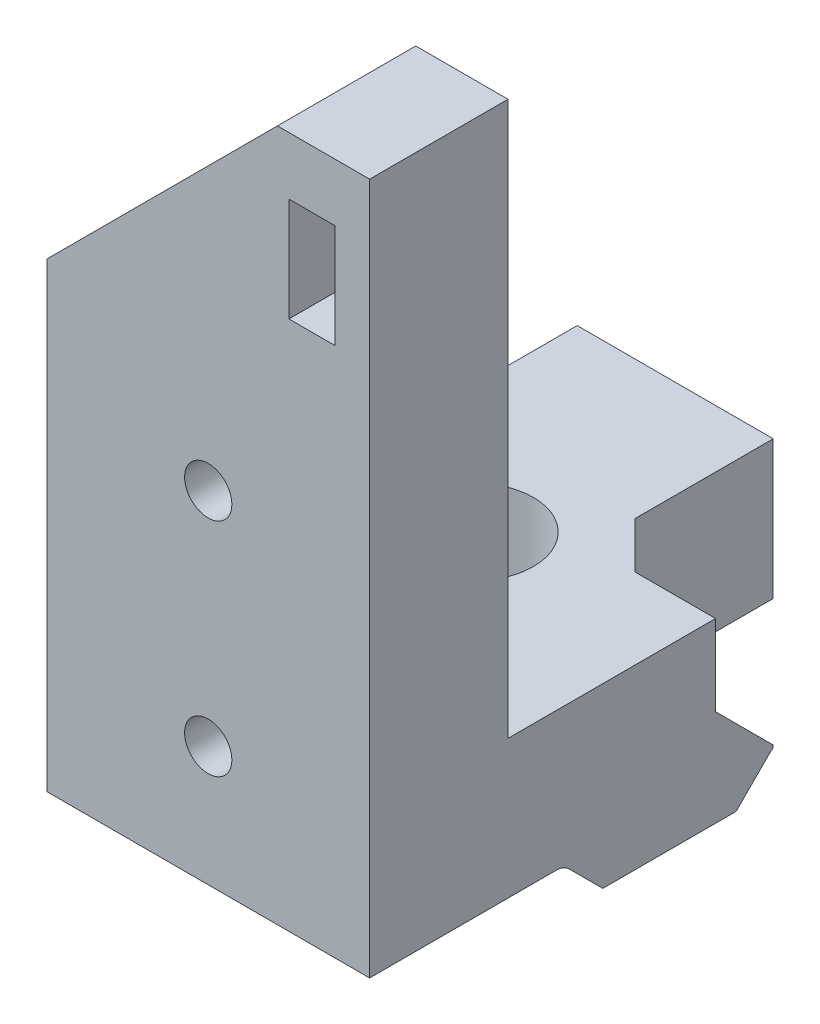
SolidWorks part; units mm, degrees
ref_plane "Front Plane" through (0, 0, 0) normal (0, 0, 1) x (1, 0, 0)
ref_plane "Top Plane" through (0, 0, 0) normal (0, 1, 0) x (1, 0, 0)
ref_plane "Right Plane" through (0, 0, 0) normal (1, 0, 0) x (0, 0, -1)
sketch "Sketch1" plane through (32.3643, 0, 0) normal (1, 0, 0) x (0, 0, -1)
  line L0 (-10.7659, 34.0751) -> (-4.9859, 34.0751)
  line L1 (-17.8759, 35.7651) -> (2.1241, 35.7651)
  line L2 (-17.8759, 35.7651) -> (-17.8759, 41.7651)
  line L3 (-17.8759, 41.7651) -> (2.1241, 41.7651)
  line L4 (2.1241, 35.7651) -> (2.1241, 41.7651)
  line L52 (-5.5365, 22.3651) -> (-2.3759, 19.2044)
  line L53 (-2.3759, 19.2044) -> (-2.3759, 17.5651)
  line L54 (-2.3759, 17.5651) -> (-4.9859, 17.5651)
  line L55 (-4.9859, 17.5651) -> (-4.9859, 17.4551)
  line L56 (-4.9859, 17.4551) -> (-3.5273, 15.9964)
  line L57 (-2.9686, 15.7651) -> (0.6241, 15.7651)
  line L58 (2.1241, 17.2651) -> (2.1241, 20.8578)
  line L59 (1.8927, 21.4164) -> (0.4341, 22.8751)
  line L60 (0.4341, 22.8751) -> (0.3241, 22.8751)
  line L61 (0.3241, 22.8751) -> (0.3241, 20.2651)
  line L62 (0.3241, 20.2651) -> (-1.3152, 20.2651)
  line L63 (-1.3152, 20.2651) -> (-4.4759, 23.4257)
  line L64 (-4.4759, 23.4257) -> (-4.4759, 28.1044)
  line L65 (-4.4759, 28.1044) -> (-1.3152, 31.2651)
  line L66 (-1.3152, 31.2651) -> (0.3241, 31.2651)
  line L67 (0.3241, 31.2651) -> (0.3241, 28.6551)
  line L68 (0.3241, 28.6551) -> (0.4341, 28.6551)
  line L69 (0.4341, 28.6551) -> (1.8927, 30.1137)
  line L70 (2.1241, 30.6723) -> (2.1241, 34.2651)
  line L71 (0.6241, 35.7651) -> (-2.9686, 35.7651)
  line L72 (-3.5273, 35.5337) -> (-4.9859, 34.0751)
  line L73 (-4.9859, 34.0751) -> (-4.9859, 33.9651)
  line L74 (-4.9859, 33.9651) -> (-2.3759, 33.9651)
  line L75 (-2.3759, 33.9651) -> (-2.3759, 32.3257)
  line L76 (-2.3759, 32.3257) -> (-5.5365, 29.1651)
  line L77 (-5.5365, 29.1651) -> (-10.2152, 29.1651)
  line L78 (-10.2152, 29.1651) -> (-13.3759, 32.3257)
  line L79 (-13.3759, 32.3257) -> (-13.3759, 33.9651)
  line L80 (-13.3759, 33.9651) -> (-10.7659, 33.9651)
  line L81 (-10.7659, 33.9651) -> (-10.7659, 34.0751)
  line L82 (-10.7659, 34.0751) -> (-12.2245, 35.5337)
  line L83 (-12.7831, 35.7651) -> (-16.3759, 35.7651)
  line L84 (-17.8759, 34.2651) -> (-17.8759, 30.6723)
  line L85 (-17.6445, 30.1137) -> (-16.1859, 28.6551)
  line L86 (-16.1859, 28.6551) -> (-16.0759, 28.6551)
  line L87 (-16.0759, 28.6551) -> (-16.0759, 31.2651)
  line L88 (-16.0759, 31.2651) -> (-14.4365, 31.2651)
  line L89 (-14.4365, 31.2651) -> (-11.2759, 28.1044)
  line L90 (-11.2759, 28.1044) -> (-11.2759, 23.4257)
  line L91 (-11.2759, 23.4257) -> (-14.4365, 20.2651)
  line L92 (-14.4365, 20.2651) -> (-16.0759, 20.2651)
  line L93 (-16.0759, 20.2651) -> (-16.0759, 22.8751)
  line L94 (-16.0759, 22.8751) -> (-16.1859, 22.8751)
  line L95 (-16.1859, 22.8751) -> (-17.6445, 21.4164)
  line L96 (-17.8759, 20.8578) -> (-17.8759, 17.2651)
  line L97 (-16.3759, 15.7651) -> (-12.7831, 15.7651)
  line L98 (-12.2245, 15.9964) -> (-10.7659, 17.4551)
  line L99 (-10.7659, 17.4551) -> (-10.7659, 17.5651)
  line L100 (-10.7659, 17.5651) -> (-13.3759, 17.5651)
  line L101 (-13.3759, 17.5651) -> (-13.3759, 19.2044)
  line L102 (-13.3759, 19.2044) -> (-10.2152, 22.3651)
  line L103 (-10.2152, 22.3651) -> (-5.5365, 22.3651)
  line L104 (-5.5365, 22.3651) -> (-2.3759, 19.2044)
  line L105 (-2.3759, 19.2044) -> (-2.3759, 17.5651)
  line L106 (-2.3759, 17.5651) -> (-4.9859, 17.5651)
  line L107 (-4.9859, 17.5651) -> (-4.9859, 17.4551)
  line L108 (-4.9859, 17.4551) -> (-3.5273, 15.9964)
  line L109 (-2.9686, 15.7651) -> (0.6241, 15.7651)
  line L110 (2.1241, 17.2651) -> (2.1241, 20.8578)
  line L111 (1.8927, 21.4164) -> (0.4341, 22.8751)
  line L112 (0.4341, 22.8751) -> (0.3241, 22.8751)
  line L113 (0.3241, 22.8751) -> (0.3241, 20.2651)
  line L114 (0.3241, 20.2651) -> (-1.3152, 20.2651)
  line L115 (-1.3152, 20.2651) -> (-4.4759, 23.4257)
  line L116 (-4.4759, 23.4257) -> (-4.4759, 28.1044)
  line L117 (-4.4759, 28.1044) -> (-1.3152, 31.2651)
  line L118 (-1.3152, 31.2651) -> (0.3241, 31.2651)
  line L119 (0.3241, 31.2651) -> (0.3241, 28.6551)
  line L120 (0.3241, 28.6551) -> (0.4341, 28.6551)
  line L121 (0.4341, 28.6551) -> (1.8927, 30.1137)
  line L122 (2.1241, 30.6723) -> (2.1241, 34.2651)
  line L123 (0.6241, 35.7651) -> (-2.9686, 35.7651)
  line L124 (-3.5273, 35.5337) -> (-4.9859, 34.0751)
  line L125 (-4.9859, 34.0751) -> (-4.9859, 33.9651)
  line L126 (-4.9859, 33.9651) -> (-2.3759, 33.9651)
  line L127 (-2.3759, 33.9651) -> (-2.3759, 32.3257)
  line L128 (-2.3759, 32.3257) -> (-5.5365, 29.1651)
  line L129 (-5.5365, 29.1651) -> (-10.2152, 29.1651)
  line L130 (-10.2152, 29.1651) -> (-13.3759, 32.3257)
  line L131 (-13.3759, 32.3257) -> (-13.3759, 33.9651)
  line L132 (-13.3759, 33.9651) -> (-10.7659, 33.9651)
  line L133 (-10.7659, 33.9651) -> (-10.7659, 34.0751)
  line L134 (-10.7659, 34.0751) -> (-12.2245, 35.5337)
  line L135 (-12.7831, 35.7651) -> (-16.3759, 35.7651)
  line L136 (-17.8759, 34.2651) -> (-17.8759, 30.6723)
  line L137 (-17.6445, 30.1137) -> (-16.1859, 28.6551)
  line L138 (-16.1859, 28.6551) -> (-16.0759, 28.6551)
  line L139 (-16.0759, 28.6551) -> (-16.0759, 31.2651)
  line L140 (-16.0759, 31.2651) -> (-14.4365, 31.2651)
  line L141 (-14.4365, 31.2651) -> (-11.2759, 28.1044)
  line L142 (-11.2759, 28.1044) -> (-11.2759, 23.4257)
  line L143 (-11.2759, 23.4257) -> (-14.4365, 20.2651)
  line L144 (-14.4365, 20.2651) -> (-16.0759, 20.2651)
  line L145 (-16.0759, 20.2651) -> (-16.0759, 22.8751)
  line L146 (-16.0759, 22.8751) -> (-16.1859, 22.8751)
  line L147 (-16.1859, 22.8751) -> (-17.6445, 21.4164)
  line L148 (-17.8759, 20.8578) -> (-17.8759, 17.2651)
  line L149 (-16.3759, 15.7651) -> (-12.7831, 15.7651)
  line L150 (-12.2245, 15.9964) -> (-10.7659, 17.4551)
  line L151 (-10.7659, 17.4551) -> (-10.7659, 17.5651)
  line L152 (-10.7659, 17.5651) -> (-13.3759, 17.5651)
  line L153 (-13.3759, 17.5651) -> (-13.3759, 19.2044)
  line L154 (-13.3759, 19.2044) -> (-10.2152, 22.3651)
  line L155 (-10.2152, 22.3651) -> (-5.5365, 22.3651)
  arc A12 (-3.5273, 15.9964) -> (-2.9686, 15.7651) centre (-2.9686, 16.5551) ccw
  arc A13 (0.6241, 15.7651) -> (2.1241, 17.2651) centre (0.6241, 17.2651) ccw
  arc A14 (2.1241, 20.8578) -> (1.8927, 21.4164) centre (1.3341, 20.8578) ccw
  arc A15 (1.8927, 30.1137) -> (2.1241, 30.6723) centre (1.3341, 30.6723) ccw
  arc A16 (2.1241, 34.2651) -> (0.6241, 35.7651) centre (0.6241, 34.2651) ccw
  arc A17 (-2.9686, 35.7651) -> (-3.5273, 35.5337) centre (-2.9686, 34.9751) ccw
  arc A18 (-12.2245, 35.5337) -> (-12.7831, 35.7651) centre (-12.7831, 34.9751) ccw
  arc A19 (-16.3759, 35.7651) -> (-17.8759, 34.2651) centre (-16.3759, 34.2651) ccw
  arc A20 (-17.8759, 30.6723) -> (-17.6445, 30.1137) centre (-17.0859, 30.6723) ccw
  arc A21 (-17.6445, 21.4164) -> (-17.8759, 20.8578) centre (-17.0859, 20.8578) ccw
  arc A22 (-17.8759, 17.2651) -> (-16.3759, 15.7651) centre (-16.3759, 17.2651) ccw
  arc A23 (-12.7831, 15.7651) -> (-12.2245, 15.9964) centre (-12.7831, 16.5551) ccw
  arc A24 (-3.5273, 15.9964) -> (-2.9686, 15.7651) centre (-2.9686, 16.5551) ccw
  arc A25 (0.6241, 15.7651) -> (2.1241, 17.2651) centre (0.6241, 17.2651) ccw
  arc A26 (2.1241, 20.8578) -> (1.8927, 21.4164) centre (1.3341, 20.8578) ccw
  arc A27 (1.8927, 30.1137) -> (2.1241, 30.6723) centre (1.3341, 30.6723) ccw
  arc A28 (2.1241, 34.2651) -> (0.6241, 35.7651) centre (0.6241, 34.2651) ccw
  arc A29 (-2.9686, 35.7651) -> (-3.5273, 35.5337) centre (-2.9686, 34.9751) ccw
  arc A30 (-12.2245, 35.5337) -> (-12.7831, 35.7651) centre (-12.7831, 34.9751) ccw
  arc A31 (-16.3759, 35.7651) -> (-17.8759, 34.2651) centre (-16.3759, 34.2651) ccw
  arc A32 (-17.8759, 30.6723) -> (-17.6445, 30.1137) centre (-17.0859, 30.6723) ccw
  arc A33 (-17.6445, 21.4164) -> (-17.8759, 20.8578) centre (-17.0859, 20.8578) ccw
  arc A34 (-17.8759, 17.2651) -> (-16.3759, 15.7651) centre (-16.3759, 17.2651) ccw
  arc A35 (-12.7831, 15.7651) -> (-12.2245, 15.9964) centre (-12.7831, 16.5551) ccw
  dimension "D2" = 6
  dimension "D1" = 0
extrude "Boss-Extrude1" add sketch "Sketch1" along normal blind 14 contours L1 L4 L3 L2 | A30 L134 L0 L124 A29 L1
sketch "Sketch2" plane through (0, 34.0751, 0) normal (0, -1, 0) x (1, 0, 0)
  line L0 (46.3643, 7.8759) -> (32.3643, 7.8759) construction
  line L1 (32.3643, 10.7659) -> (32.3643, 4.9859) construction
  line L2 (46.3643, 10.7659) -> (46.3643, 4.9859) construction
  circle A0 centre (37.8643, 7.8759) radius 2.6
  dimension "D1" = 5.2
  dimension "D2" = 5.5
extrude "Cut-Extrude1" cut sketch "Sketch2" against normal up to next
sketch "Sketch3" plane through (0, 0, 17.8759) normal (0, 0, 1) x (1, 0, 0)
  line L1 (32.3643, 35.7651) -> (46.3643, 35.7651)
  line L2 (32.3643, 35.7651) -> (32.3643, 55.7651)
  line L3 (32.3643, 55.7651) -> (46.3643, 55.7651)
  line L4 (46.3643, 35.7651) -> (46.3643, 55.7651)
  line L6 (46.3643, 35.7651) -> (46.3643, 41.7651) construction
  dimension "D1" = 20
extrude "Boss-Extrude2" add sketch "Sketch3" along normal blind 3 and the other way blind 3
sketch "Sketch4" plane through (0, 0, 20.8759) normal (0, 0, 1) x (1, 0, 0)
  line L0 (32.3643, 55.7651) -> (32.3643, 35.7651) construction
  line L1 (32.3643, 35.7651) -> (46.3643, 35.7651) construction
  circle A0 centre (39.3643, 50.5651) radius 1.025
  circle A1 centre (39.3643, 40.9651) radius 1.025
  dimension "D1" = 7
  dimension "D5" = 2.05
  dimension "D6" = 2.05
  dimension "D2" = 7
  dimension "D3" = 9.6
  dimension "D4" = 5.2
extrude "Cut-Extrude4" cut sketch "Sketch4" against normal blind 6
sketch "Sketch5" plane through (0, 41.7651, 0) normal (0, 1, 0) x (1, 0, 0)
  line L1 (40.8643, -5.8759) -> (46.3643, -5.8759)
  line L2 (40.8643, -5.8759) -> (40.8643, 2.1241)
  line L3 (40.8643, 2.1241) -> (46.3643, 2.1241)
  line L4 (46.3643, -5.8759) -> (46.3643, 2.1241)
  dimension "D1" = 5.5
  dimension "D2" = 8
extrude "Cut-Extrude5" cut sketch "Sketch5" against normal up to surface (6 mm away) up to face at (39.3643, 35.7651, 0.4223)
chamfer "Chamfer1" distance 2 angle 45 1 edges at (40.8643, 38.7651, 5.8759)
chamfer "Chamfer2" distance 2.5 angle 45 1 edges at (44.6143, 35.7651, 5.8759)
sketch "Sketch6" plane through (0, 35.7651, 0) normal (0, 1, 0) x (1, 0, 0)
  line L4 (40.8643, -2.9686) -> (40.8643, -3.3759)
  line L5 (40.8643, -3.3759) -> (46.3643, -3.3759)
  line L6 (46.3643, -3.3759) -> (46.3643, -2.9686)
  line L7 (46.3643, -2.9686) -> (40.8643, -2.9686)
  line L8 (40.8643, -2.9686) -> (40.8643, -3.3759)
  line L9 (40.8643, -3.3759) -> (46.3643, -3.3759)
  line L10 (46.3643, -3.3759) -> (46.3643, -2.9686)
  line L11 (46.3643, -2.9686) -> (40.8643, -2.9686)
  dimension "D1" = 0
extrude "Cut-Extrude6" cut sketch "Sketch6" against normal through all
sketch "Sketch7" plane through (0, 0, 20.8759) normal (0, 0, 1) x (1, 0, 0)
  line L0 (46.3643, 55.7651) -> (46.3643, 65.7651)
  line L1 (46.3643, 65.7651) -> (42.3643, 65.7651)
  line L2 (42.3643, 65.7651) -> (32.3643, 55.7651)
  line L3 (32.3643, 55.7651) -> (46.3643, 55.7651)
  line L5 (42.8643, 63.2651) -> (44.8643, 63.2651)
  line L6 (42.8643, 63.2651) -> (42.8643, 58.7651)
  line L7 (42.8643, 58.7651) -> (44.8643, 58.7651)
  line L8 (44.8643, 63.2651) -> (44.8643, 58.7651)
  dimension "D1" = 45
  dimension "D2" = 10
  dimension "D3" = 2
  dimension "D4" = 4.5
  dimension "D5" = 1.5
  dimension "D6" = 2.5
extrude "Boss-Extrude3" add sketch "Sketch7" against normal up to surface (6 mm away) up to face at (39.3643, 46.4692, 14.8759)
